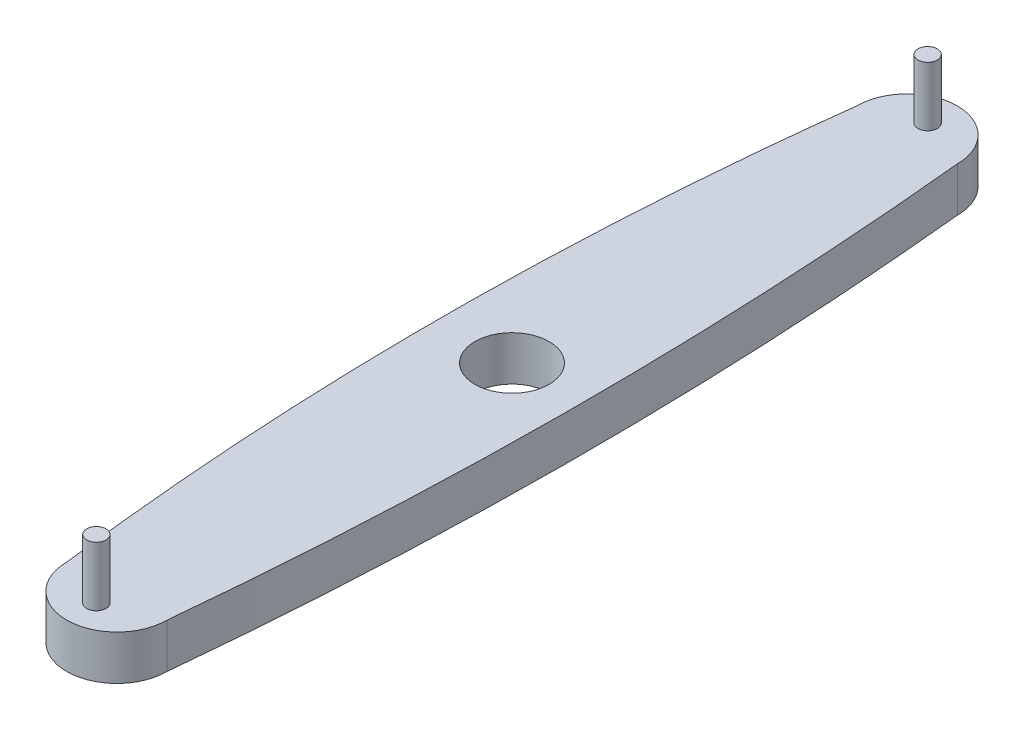
SolidWorks part; units mm, degrees
material "AISI 1020 Steel, Cold Rolled"
ref_plane "Front Plane" through (0, 0, 0) normal (0, 0, 1) x (1, 0, 0)
ref_plane "Top Plane" through (0, 0, 0) normal (0, 1, 0) x (1, 0, 0)
ref_plane "Right Plane" through (0, 0, 0) normal (1, 0, 0) x (0, 0, -1)
sketch "Sketch1" plane through (0, 0, 0) normal (0, 1, 0) x (1, 0, 0)
  line L0 (-77.618, 0) -> (-33.8206, 266.1794)
  line L1 (0, -300) -> (0, -318.9637) construction
  line L2 (33.8206, 266.1794) -> (72.1766, 0)
  line L3 (-160.5166, 0) -> (105.4185, 0) construction
  line L4 (0, -266.1794) -> (0, 266.1794) construction
  line L5 (0, 300) -> (0, 318.9637) construction
  line L6 (33.8206, -266.1794) -> (72.1766, 0)
  line L7 (-77.618, 0) -> (-33.8206, -266.1794)
  arc A0 (33.8206, 266.1794) -> (-33.8206, 266.1794) centre (0, 266.1794) ccw
  arc A1 (33.8206, -266.1794) -> (-33.8206, -266.1794) centre (0, -266.1794) cw
  point P14 (0, 0)
  dimension "D1" = 600
extrude "Boss-Extrude1" add sketch "Sketch1" along normal blind 30
sketch "Sketch2" plane through (0, 30, 0) normal (0, 1, 0) x (1, 0, 0)
  circle A0 centre (0, 0) radius 25
  dimension "D1" = 50
extrude "Cut-Extrude1" cut sketch "Sketch2" against normal blind 30
sketch "Sketch3" plane through (0, 30, 0) normal (0, 1, 0) x (1, 0, 0)
  circle A0 centre (0, -280) radius 6.505
  arc A1 (-33.8206, -266.1794) -> (33.8206, -266.1794) centre (0, -266.1794) ccw construction
  point P5 (0, -300)
  dimension "D2" = 13.01
  dimension "D1" = 20
extrude "Boss-Extrude2" add sketch "Sketch3" along normal blind 40
mirror "Mirror1" about plane through (0, 0, 0) normal (0, 0, 1) of "Boss-Extrude2"
sketch "Sketch4" plane through (0, 30, 0) normal (0, 1, 0) x (1, 0, 0)
  line L0 (33.8206, -266.1794) -> (72.1766, 0) construction
  line L1 (-77.618, 0) -> (-33.8206, -266.1794) construction
  line L2 (-77.618, 0) -> (-33.8206, -266.1794)
  line L3 (72.1766, 0) -> (33.8206, 266.1794) construction
  line L4 (72.1766, 0) -> (33.8206, 266.1794)
  line L5 (33.8206, -266.1794) -> (72.1766, 0)
  spline S0 degree 1 poles (-33.8206, 266.1794) (-77.618, 0) knots 0 0 1 1
  spline S1 degree 2 poles (-33.8206, 266.1794) (-66.842, 0) (-33.8206, -266.1794) knots 0 0 0 1 1 1
  spline S2 degree 2 poles (33.8206, 266.1794) (60.1279, -0.0302) (33.8206, -266.1794) knots 0 0 0 1 1 1
  point P8 (0, 0)
  point P11 (50.2113, 0)
  point P12 (51.579, -3.8336)
  point P16 (-50.3313, 0)
  point P17 (46.9671, -6.1959)
  point P18 (33.78, -267.8359)
extrude "Cut-Extrude2" cut sketch "Sketch4" against normal blind 40
